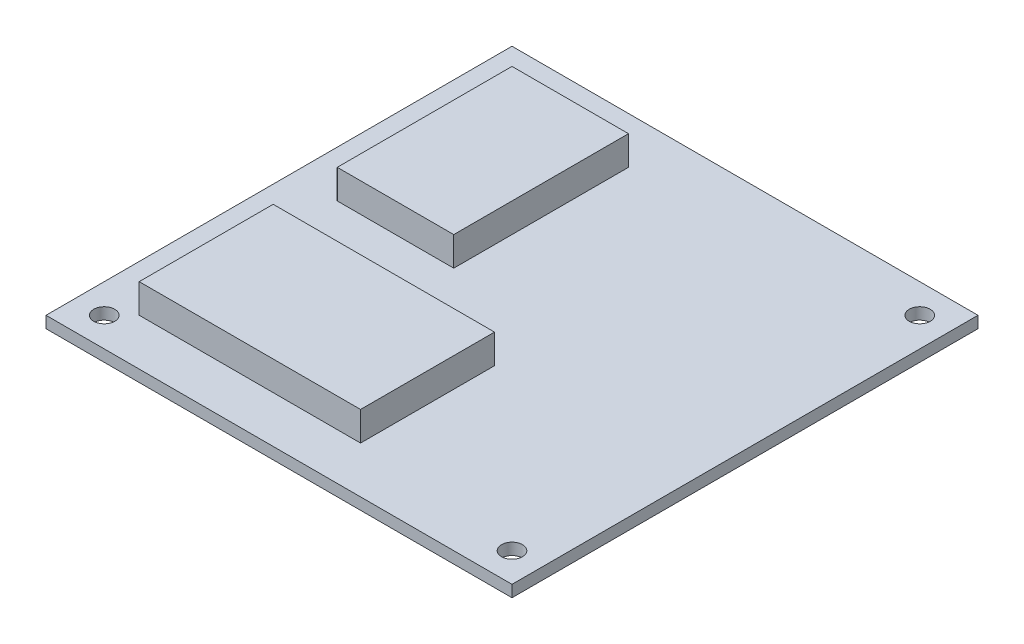
SolidWorks part; units mm, degrees
ref_plane "Front Plane" through (0, 0, 0) normal (0, 0, 1) x (1, 0, 0)
ref_plane "Top Plane" through (0, 0, 0) normal (0, 1, 0) x (1, 0, 0)
ref_plane "Right Plane" through (0, 0, 0) normal (1, 0, 0) x (0, 0, -1)
sketch "Sketch1" plane through (0, 0, 0) normal (0, 1, 0) x (1, 0, 0)
  line L1 (0, 0) -> (80, 0)
  line L2 (0, 0) -> (0, 80)
  line L3 (0, 80) -> (80, 80)
  line L4 (80, 0) -> (80, 80)
  dimension "D1" = 80
  dimension "D2" = 80
extrude "PCB" add sketch "Sketch1" along normal blind 2
sketch "Sketch2" plane through (0, 2, 0) normal (0, 1, 0) x (1, 0, 0)
  line L0 (80, 80) -> (0, 80) construction
  line L1 (0, 80) -> (0, 0) construction
  circle A0 centre (5, 75) radius 1.8
  dimension "D1" = 3.6
  dimension "D2" = 5
  dimension "D3" = 5
extrude "Attachment Holes" cut sketch "Sketch2" against normal through all
pattern_linear "LPattern1" count 2 spacing 70 along (1, 0, 0) count 2 spacing 70 along (0, 0, 1) of "Attachment Holes"
sketch "Sketch3" plane through (0, 2, 0) normal (0, 1, 0) x (1, 0, 0)
  line L0 (80, 80) -> (0, 80) construction
  line L1 (8, 72) -> (28, 72)
  line L2 (8, 72) -> (8, 42)
  line L3 (8, 42) -> (28, 42)
  line L4 (28, 72) -> (28, 42)
  line L5 (0, 80) -> (0, 0) construction
  dimension "D1" = 30
  dimension "D2" = 20
  dimension "D3" = 8
  dimension "D4" = 8
extrude "GPS" add sketch "Sketch3" along normal blind 5
sketch "Sketch4" plane through (0, 2, 0) normal (0, 1, 0) x (1, 0, 0)
  line L0 (0, 0) -> (80, 0) construction
  line L1 (8, 31) -> (46, 31)
  line L2 (8, 31) -> (8, 8)
  line L3 (8, 8) -> (46, 8)
  line L4 (46, 31) -> (46, 8)
  line L5 (0, 80) -> (0, 0) construction
  dimension "D1" = 38
  dimension "D2" = 23
  dimension "D3" = 8
  dimension "D4" = 8
extrude "IMU" add sketch "Sketch4" along normal blind 5
